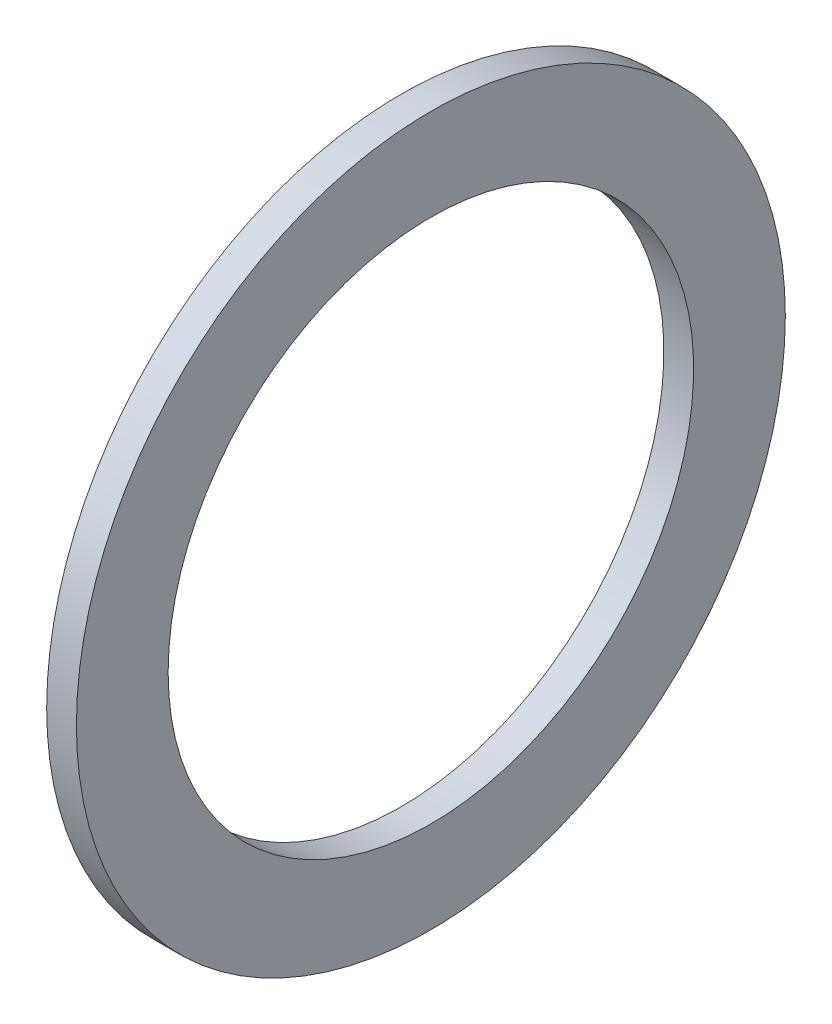
SolidWorks part; units mm, degrees
ref_plane "Front Plane" through (0, 0, 0) normal (0, 0, 1) x (1, 0, 0)
ref_plane "Top Plane" through (0, 0, 0) normal (0, 1, 0) x (1, 0, 0)
ref_plane "Right Plane" through (0, 0, 0) normal (1, 0, 0) x (0, 0, -1)
sketch "Sketch1" plane through (0, 0, 0) normal (0, 0, 1) x (1, 0, 0)
  line L0 (-43.7166, 0) -> (79.6876, 0) construction
  line L2 (0, -13.462) -> (1.524, -13.462)
  line L3 (0, -13.462) -> (0, -18.161)
  line L4 (0, -18.161) -> (1.524, -18.161)
  line L5 (1.524, -13.462) -> (1.524, -18.161)
  dimension "A" = 26.924
  dimension "B" = 36.322
  dimension "C" = 1.524
revolve "Revolve1" add sketch "Sketch1" angle 360 about L0
sketch "Sketch2" [suppressed] plane through (0, 0, 0) normal (0, 0, 1) x (1, 0, 0)
  line L0 (-34.685, 0) -> (47.6686, 0) construction
  circle A0 centre (2.54, -5.715) radius 0.762
  dimension "D1" = 2.54
  dimension "E" = 2.032
  dimension "D" = 22.098
revolve "Revolve3" [suppressed] add sketch "Sketch2" angle 360 about L0
